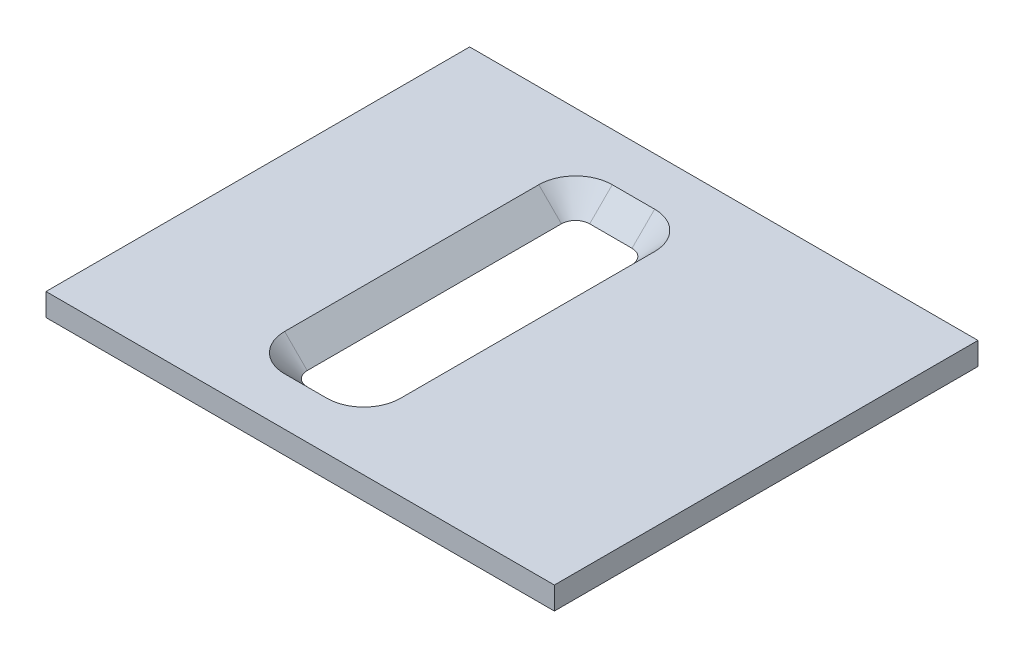
SolidWorks part; units mm, degrees
material "6061-T4 (SS)"
ref_plane "Front Plane" through (0, 0, 0) normal (0, 0, 1) x (1, 0, 0)
ref_plane "Top Plane" through (0, 0, 0) normal (0, 1, 0) x (1, 0, 0)
ref_plane "Right Plane" through (0, 0, 0) normal (1, 0, 0) x (0, 0, -1)
sketch "Sketch2" plane through (0, 0, 0) normal (0, 1, 0) x (1, 0, 0)
  line L0 (3, 0) -> (0, 0) construction
  line L5 (-15, 15) -> (21, 15)
  line L6 (-15, 15) -> (-15, -15)
  line L7 (-15, -15) -> (21, -15)
  line L8 (21, 15) -> (21, -15)
  line L9 (-15, 15) -> (21, -15) construction
  line L10 (-15, -15) -> (21, 15) construction
  dimension "D1" = 36
  dimension "D2" = 30
  dimension "D3" = 3
extrude "Boss-Extrude1" add sketch "Sketch2" along normal blind 1.6002
sketch "Sketch4" plane through (0, 0, 0) normal (0, 1, 0) x (1, 0, 0)
  line L1 (1.5, -10) -> (-1.5, -10)
  line L2 (2.5, -9) -> (2.5, 9)
  line L3 (1.5, 10) -> (-1.5, 10)
  line L4 (-2.5, -9) -> (-2.5, 9)
  line L5 (2.5, -10) -> (-2.5, 10) construction
  line L6 (2.5, 10) -> (-2.5, -10) construction
  arc A0 (1.5, -10) -> (2.5, -9) centre (1.5, -9) ccw
  arc A1 (2.5, 9) -> (1.5, 10) centre (1.5, 9) ccw
  arc A2 (-1.5, 10) -> (-2.5, 9) centre (-1.5, 9) ccw
  arc A3 (-1.5, -10) -> (-2.5, -9) centre (-1.5, -9) cw
  point P0 (0, 0)
  dimension "D3" = 1
  dimension "D1" = 20
  dimension "D2" = 5
extrude "Cut-Extrude4" cut sketch "Sketch4" along normal through all draft 45 draft outward yes
sketch3d "3DSketch1"
  line L0 (0, 2, 0) -> (0, 20.7837, 0) construction
hole_wizard "#2 Clearance Hole1" positions "Sketch7" profile "Sketch6" hole size "#2" standard "ANSI Inch"
sketch "Sketch7" plane through (0, 0, 0) normal (0, -1, 0) x (-1, 0, 0)
  circle A0 centre (-14.5138, 10) radius 0.889 construction
  circle A1 centre (-14.5138, -10) radius 0.889 construction
  point P0 (-14.5138, -10)
  point P2 (-14.5138, 10)
sketch "Sketch6" plane through (14.5138, 0, 10) normal (1, 0, 0) x (0, 0, -1)
  line L0 (0, 0) -> (0, 1.6002)
  line L1 (0, 1.6002) -> (1.2192, 1.6002)
  line L2 (1.2192, 1.6002) -> (1.2192, 0)
  line L5 (1.2192, 0) -> (0, 0)
  line L11 (0, -6.35) -> (0, 107.95) construction
  dimension "Thru Hole Dia." = 2.4384
  dimension "Thru Hole Depth" = 2
hole_wizard "#0 Clearance Hole1" positions "Sketch8" profile "Sketch10" hole size "#0" standard "ANSI Inch"
sketch "Sketch8" plane through (0, 0, 0) normal (0, -1, 0) x (-1, 0, 0)
  line L1 (12, -12) -> (12, 0) construction
  line L5 (15, 15) -> (15, -15) construction
  line L7 (12, 0) -> (15, 0) construction
  line L9 (15, -15) -> (-21, -15) construction
  point P0 (12, -12)
  dimension "D1" = 3
  dimension "D2" = 3
sketch "Sketch10" plane through (-12, 0, 12) normal (1, 0, 0) x (0, 0, -1)
  line L0 (0, 0) -> (0, 1.6002)
  line L1 (0, 1.6002) -> (0.889, 1.6002)
  line L2 (0.889, 1.6002) -> (0.889, 0)
  line L5 (0.889, 0) -> (0, 0)
  line L11 (0, -6.35) -> (0, 107.95) construction
  dimension "Thru Hole Dia." = 1.778
  dimension "Thru Hole Depth" = 1.6002
